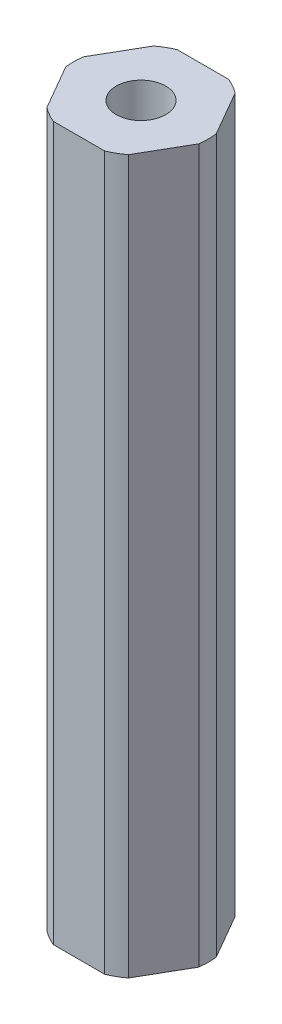
SolidWorks part; units mm, degrees
material "7075-T6 (SN)"
ref_plane "Front Plane" through (0, 0, 0) normal (0, 0, 1) x (1, 0, 0)
ref_plane "Top Plane" through (0, 0, 0) normal (0, 1, 0) x (1, 0, 0)
ref_plane "Right Plane" through (0, 0, 0) normal (1, 0, 0) x (0, 0, -1)
sketch "Sketch1" plane through (0, 0, 0) normal (0, 1, 0) x (1, 0, 0)
  line L1 (4.1818, -5.457) -> (6.8168, -0.893)
  line L2 (6.8168, 0.893) -> (4.1818, 5.457)
  line L3 (2.635, 6.35) -> (-2.635, 6.35)
  line L4 (-4.1818, 5.457) -> (-6.8168, 0.893)
  line L5 (-6.8168, -0.893) -> (-4.1818, -5.457)
  line L6 (-2.635, -6.35) -> (2.635, -6.35)
  circle A0 centre (0, 0) radius 6.35 construction
  arc A1 (2.635, -6.35) -> (4.1818, -5.457) centre (0, 0) ccw
  arc A2 (6.8168, -0.893) -> (6.8168, 0.893) centre (0, 0) ccw
  arc A3 (4.1818, 5.457) -> (2.635, 6.35) centre (0, 0) ccw
  arc A4 (-2.635, 6.35) -> (-4.1818, 5.457) centre (0, 0) ccw
  arc A5 (-6.8168, 0.893) -> (-6.8168, -0.893) centre (0, 0) ccw
  arc A6 (-4.1818, -5.457) -> (-2.635, -6.35) centre (0, 0) ccw
  circle A7 centre (0, 0) radius 2.54
  dimension "D1" = 12.7
  dimension "D2" = 13.75
  dimension "D3" = 5.08
extrude "Boss-Extrude1" add sketch "Sketch1" along normal blind 73.025
